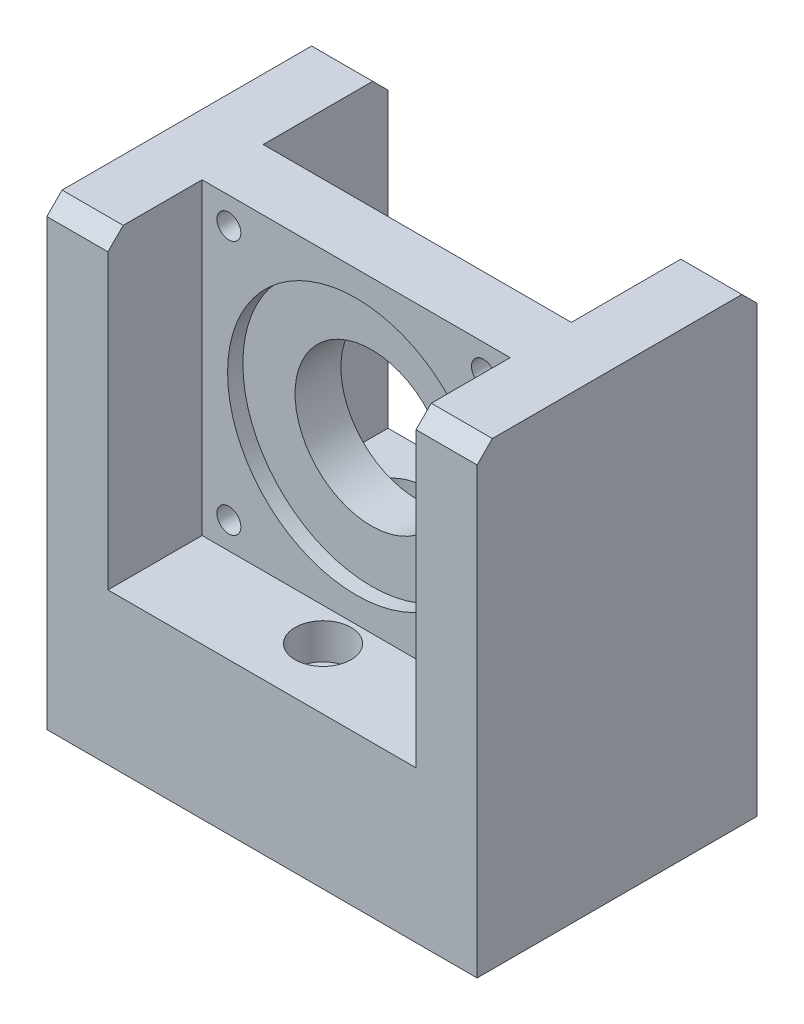
SolidWorks part; units mm, degrees
ref_plane "Front Plane" through (0, 0, 0) normal (0, 0, 1) x (1, 0, 0)
ref_plane "Top Plane" through (0, 0, 0) normal (0, 1, 0) x (1, 0, 0)
ref_plane "Right Plane" through (0, 0, 0) normal (1, 0, 0) x (0, 0, -1)
sketch "Sketch1" plane through (0, 0, 0) normal (0, 0, 1) x (1, 0, 0)
  line L1 (30.25, -30.25) -> (-30.25, -30.25)
  line L2 (30.25, -30.25) -> (30.25, 30.25)
  line L3 (30.25, 30.25) -> (-30.25, 30.25)
  line L4 (-30.25, -30.25) -> (-30.25, 30.25)
  line L5 (30.25, -30.25) -> (-30.25, 30.25) construction
  line L6 (30.25, 30.25) -> (-30.25, -30.25) construction
  line L7 (25, -25) -> (-25, -25) construction
  line L8 (25, -25) -> (25, 25) construction
  line L9 (25, 25) -> (-25, 25) construction
  line L10 (-25, -25) -> (-25, 25) construction
  line L11 (25, -25) -> (-25, 25) construction
  line L12 (25, 25) -> (-25, -25) construction
  circle A0 centre (0, 0) radius 15
  circle A1 centre (-25, 25) radius 2.35
  circle A2 centre (25, 25) radius 2.35
  circle A3 centre (25, -25) radius 2.35
  circle A4 centre (-25, -25) radius 2.35
  point P0 (0, 0)
  dimension "D2" = 30
  dimension "D4" = 4.7
  dimension "D1" = 60.5
  dimension "D3" = 50
extrude "Boss-Extrude1" add sketch "Sketch1" along normal mid plane 12
sketch "Sketch2" plane through (0, 0, 6) normal (0, 0, 1) x (1, 0, 0)
  circle A0 centre (0, 0) radius 25.25
  dimension "D1" = 50.5
extrude "Cut-Extrude1" cut sketch "Sketch2" against normal blind 3
sketch "Sketch3" plane through (0, -30.25, 0) normal (0, -1, 0) x (1, 0, 0)
  line L0 (-30.25, 6) -> (30.25, 6) construction
  line L1 (-42.25, 24.5) -> (42.25, 24.5)
  line L2 (-42.25, 24.5) -> (-42.25, -30.5)
  line L3 (-42.25, -30.5) -> (42.25, -30.5)
  line L4 (42.25, 24.5) -> (42.25, -30.5)
  line L5 (-30.25, 6) -> (-30.25, -6) construction
  line L6 (30.25, 6) -> (30.25, -6) construction
  dimension "D1" = 18.5
  dimension "D2" = 12
  dimension "D3" = 12
  dimension "D4" = 55
extrude "Boss-Extrude2" add sketch "Sketch3" along normal blind 29.75
sketch "Sketch4" plane through (30.25, 0, 0) normal (1, 0, 0) x (0, 0, -1)
  line L0 (-6, 30.25) -> (6, 30.25) construction
  line L1 (-24.5, -30.25) -> (30.5, -30.25)
  line L2 (-24.5, -30.25) -> (-24.5, 30.25)
  line L3 (-24.5, 30.25) -> (30.5, 30.25)
  line L4 (30.5, -30.25) -> (30.5, 30.25)
  line L5 (30.5, -60) -> (30.5, -30.25) construction
extrude "Boss-Extrude3" add sketch "Sketch4" along normal blind 12
sketch "Sketch5" plane through (-30.25, 0, 0) normal (-1, 0, 0) x (0, 0, 1)
  line L1 (-30.5, 30.25) -> (24.5, 30.25)
  line L2 (-30.5, 30.25) -> (-30.5, -30.25)
  line L3 (-30.5, -30.25) -> (24.5, -30.25)
  line L4 (24.5, 30.25) -> (24.5, -30.25)
extrude "Boss-Extrude4" add sketch "Sketch5" along normal blind 12
chamfer "Chamfer1" distance 3 angle 45 4 edges at (-36.25, 30.25, -30.5) (36.25, 30.25, -30.5) (36.25, 30.25, 24.5) (-36.25, 30.25, 24.5)
sketch "Sketch6" plane through (0, -30.25, 0) normal (0, 1, 0) x (1, 0, 0)
  line L0 (0, 0) -> (0, -12.5) construction
  line L1 (30.25, -24.5) -> (-30.25, -24.5) construction
  line L2 (-30.25, 30.5) -> (30.25, 30.5) construction
  circle A0 centre (0, -12.5) radius 3.05
  circle A1 centre (-17.5, 18.5) radius 3.05
  circle A2 centre (17.5, 18.5) radius 3.05
  dimension "D1" = 6.1
  dimension "D2" = 12
  dimension "D3" = 12
  dimension "D4" = 35
extrude "Cut-Extrude2" cut sketch "Sketch6" against normal through all
sketch "Sketch7" plane through (0, -30.25, 0) normal (0, 1, 0) x (1, 0, 0)
  circle A0 centre (-17.5, 18.5) radius 5.5
  circle A1 centre (17.5, 18.5) radius 5.5
  circle A2 centre (0, -12.5) radius 5.5
  dimension "D1" = 11
extrude "Cut-Extrude3" cut sketch "Sketch7" against normal blind 7
